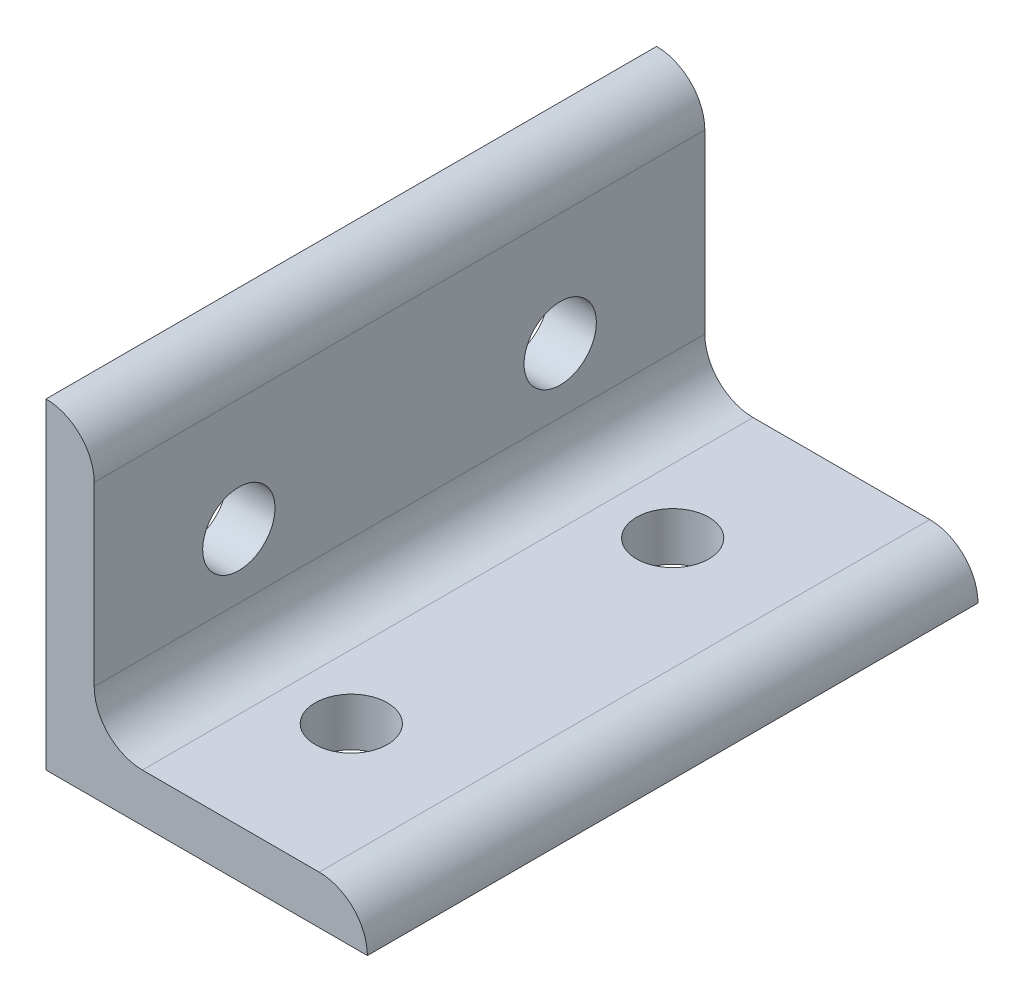
SolidWorks part; units mm, degrees
ref_plane "Front Plane" through (0, 0, 0) normal (0, 0, 1) x (1, 0, 0)
ref_plane "Top Plane" through (0, 0, 0) normal (0, 1, 0) x (1, 0, 0)
ref_plane "Right Plane" through (0, 0, 0) normal (1, 0, 0) x (0, 0, -1)
sketch "Sketch1" plane through (0, 0, 0) normal (0, 0, 1) x (1, 0, 0)
  line L0 (0, 0) -> (0, 40)
  line L1 (6, 34) -> (6, 40) construction
  line L2 (6, 34) -> (6, 12)
  line L3 (12, 6) -> (34, 6)
  line L4 (6, 40) -> (0, 40) construction
  line L5 (40, 0) -> (0, 0)
  line L6 (34, 6) -> (40, 6) construction
  line L7 (40, 6) -> (40, 0) construction
  arc A0 (6, 34) -> (0, 40) centre (0, 34) ccw
  arc A1 (40, 0) -> (34, 6) centre (34, 0) ccw
  arc A2 (6, 12) -> (12, 6) centre (12, 12) ccw
  point P10 (6, 37)
  dimension "E" = 6
  dimension "D" = 6
  dimension "C" = 40
  dimension "B" = 40
extrude "Boss-Extrude1" add sketch "Sketch1" along normal mid plane 76
sketch "Sketch2" plane through (0, 0, 0) normal (0, 1, 0) x (1, 0, 0)
  line L0 (0, -20) -> (20, -20) construction
  line L1 (0, -38) -> (0, -20) construction
  line L2 (20, -20) -> (20, 20) construction
  line L3 (0, -20) -> (0, 20) construction
  line L4 (0, 20) -> (20, 20) construction
  circle A0 centre (20, -20) radius 4.5
  circle A1 centre (20, 20) radius 4.5
extrude "Cut-Extrude1" cut sketch "Sketch2" along normal through all
sketch "Sketch3" plane through (0, 0, 0) normal (1, 0, 0) x (0, 0, -1)
  line L0 (-20, 0) -> (-20, 20) construction
  line L1 (-20, 20) -> (20, 20) construction
  line L2 (20, 20) -> (20, 0) construction
  line L3 (20, 0) -> (-20, 0) construction
  circle A0 centre (-20, 20) radius 4.5
  circle A1 centre (20, 20) radius 4.5
  dimension "D1" = 20
extrude "Cut-Extrude2" cut sketch "Sketch3" along normal through all
equation "\"E@Sketch3\" = \"E@Sketch2\""
equation "\"D1@Sketch3\" = \"D1@Sketch2\""
